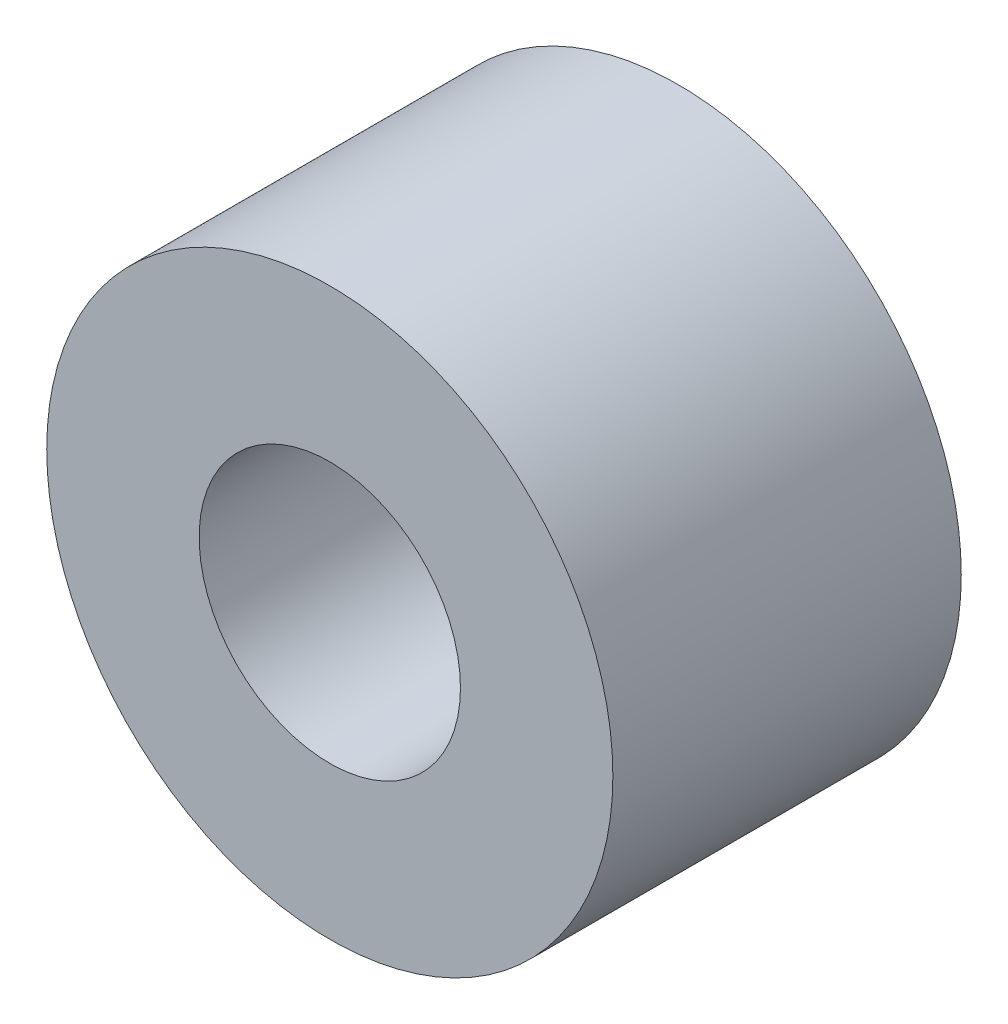
SolidWorks part; units mm, degrees
ref_plane "Front Plane" through (0, 0, 0) normal (0, 0, 1) x (1, 0, 0)
ref_plane "Top Plane" through (0, 0, 0) normal (0, 1, 0) x (1, 0, 0)
ref_plane "Right Plane" through (0, 0, 0) normal (1, 0, 0) x (0, 0, -1)
sketch "Sketch1" plane through (0, 0, 0) normal (0, 0, 1) x (1, 0, 0)
  circle A0 centre (0, 0) radius 1.5
  circle A1 centre (0, 0) radius 3.25
  dimension "D1" = 3
  dimension "D2" = 6.5
extrude "Boss-Extrude1" add sketch "Sketch1" along normal blind 4 contours A0 | A1
